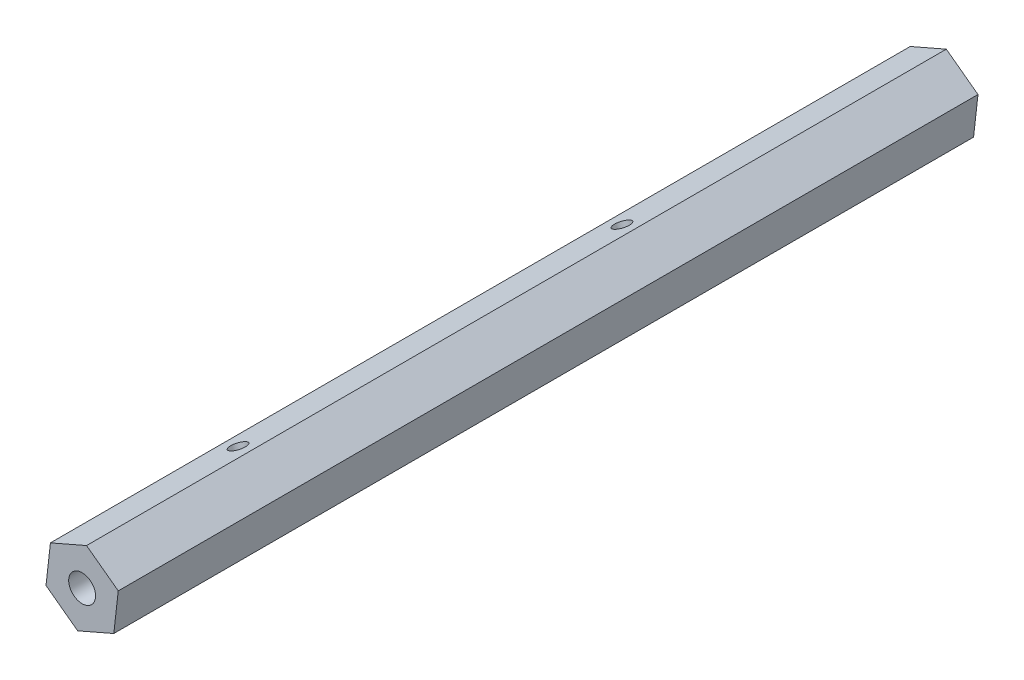
SolidWorks part; units mm, degrees
ref_plane "Plano frontal" through (0, 0, 0) normal (0, 0, 1) x (1, 0, 0)
ref_plane "Plano superior" through (0, 0, 0) normal (0, 1, 0) x (1, 0, 0)
ref_plane "Plano direito" through (0, 0, 0) normal (1, 0, 0) x (0, 0, -1)
sketch "Esboço1" plane through (0, 0, 0) normal (0, 0, 1) x (1, 0, 0)
  line L1 (5.8972, -4.3573) -> (6.7222, 2.9285)
  line L2 (6.7222, 2.9285) -> (0.8249, 7.2858)
  line L3 (0.8249, 7.2858) -> (-5.8972, 4.3573)
  line L4 (-5.8972, 4.3573) -> (-6.7222, -2.9285)
  line L5 (-6.7222, -2.9285) -> (-0.8249, -7.2858)
  line L6 (-0.8249, -7.2858) -> (5.8972, -4.3573)
  circle A0 centre (0, 0) radius 6.35 construction
  circle A1 centre (0, 0) radius 2.5
  dimension "D2" = 5
  dimension "D1" = 12.7
extrude "Ressalto-extrusão1" add sketch "Esboço1" along normal blind 160
sketch "Esboço2" plane through (-2.5361, 5.8216, 0) normal (-0.3994, 0.9168, 0) x (0.9168, 0.3994, 0)
  line L0 (3.6662, 0) -> (-3.6662, 0) construction
  circle A0 centre (0, -57) radius 1.5
  dimension "D2" = 3
  dimension "D1" = 57
extrude "Corte-extrusão1" cut sketch "Esboço2" against normal through all
sketch "Esboço3" plane through (-2.5361, 5.8216, 0) normal (-0.3994, 0.9168, 0) x (0.9168, 0.3994, 0)
  line L0 (3.6662, -160) -> (-3.6662, -160) construction
  circle A0 centre (0, -128.44) radius 1.5
  dimension "D1" = 31.56
  dimension "D2" = 3
extrude "Corte-extrusão2" cut sketch "Esboço3" against normal through all
